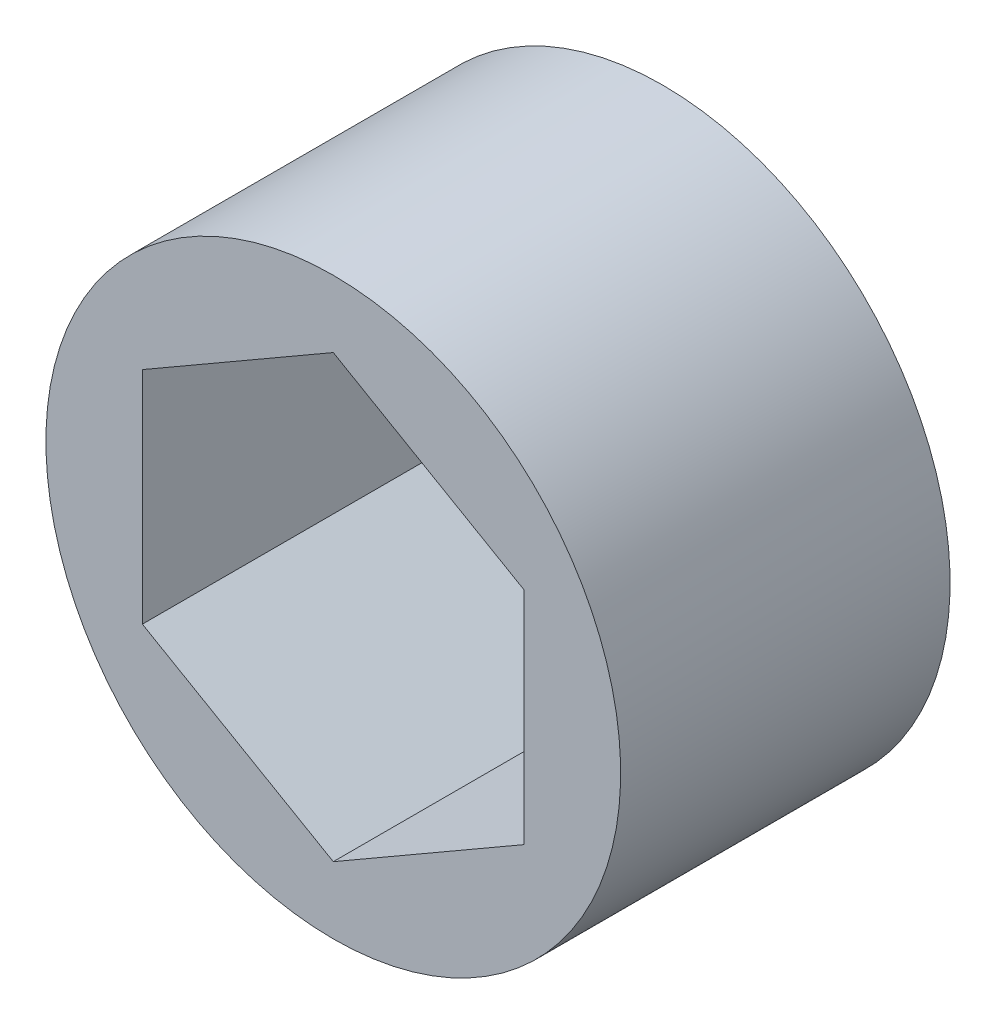
SolidWorks part; units mm, degrees
ref_plane "Front Plane" through (0, 0, 0) normal (0, 0, 1) x (1, 0, 0)
ref_plane "Top Plane" through (0, 0, 0) normal (0, 1, 0) x (1, 0, 0)
ref_plane "Right Plane" through (0, 0, 0) normal (1, 0, 0) x (0, 0, -1)
ref_plane "Plane1" through (0, 0, -1.5875) normal (0, 0, -1) x (-1, 0, 0)
sketch "Sketch1" plane through (0, 0, -1.5875) normal (0, 0, -1) x (-1, 0, 0)
  line L0 (6.477, 3.7395) -> (6.477, -3.7395)
  line L1 (6.477, -3.7395) -> (0, -7.479)
  line L2 (0, -7.479) -> (-6.477, -3.7395)
  line L3 (-6.477, -3.7395) -> (-6.477, 3.7395)
  line L4 (-6.477, 3.7395) -> (0, 7.479)
  line L5 (0, 7.479) -> (6.477, 3.7395)
  circle A0 centre (0, 0) radius 9.75
extrude "Boss-Extrude1" add sketch "Sketch1" against normal blind 11.176
